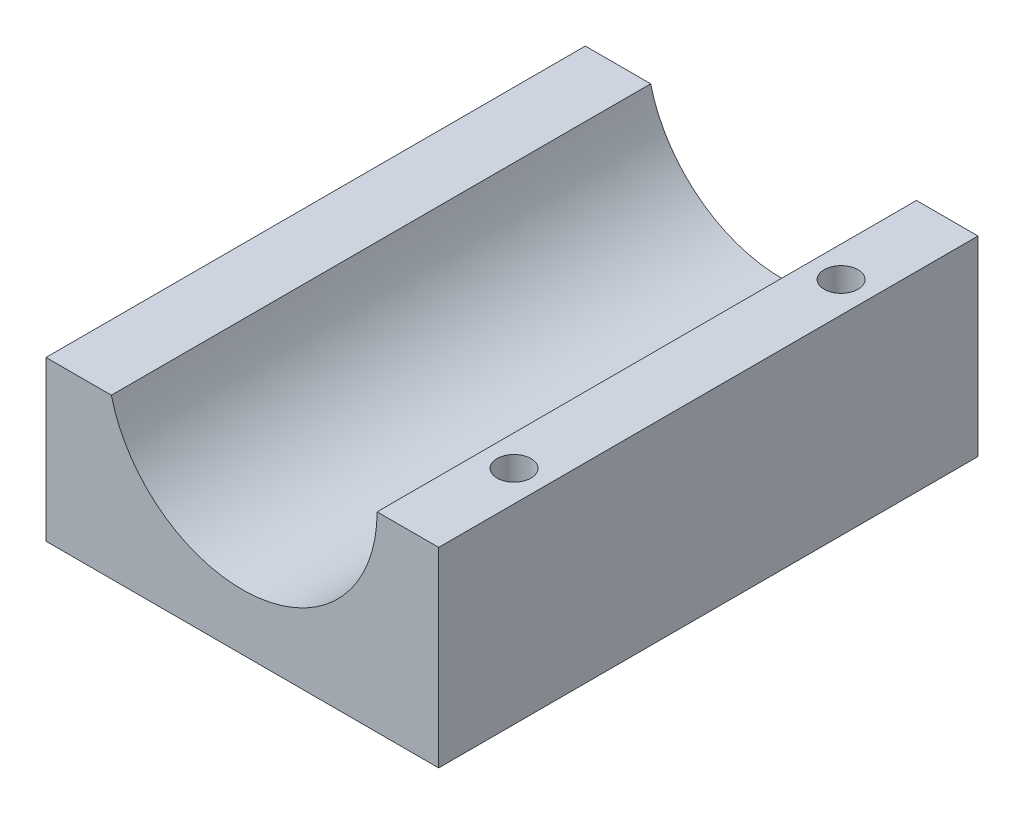
SolidWorks part; units mm, degrees
ref_plane "Front Plane" through (0, 0, 0) normal (0, 0, 1) x (1, 0, 0)
ref_plane "Top Plane" through (0, 0, 0) normal (0, 1, 0) x (1, 0, 0)
ref_plane "Right Plane" through (0, 0, 0) normal (1, 0, 0) x (0, 0, -1)
sketch "Sketch2" plane through (0, 0, 0) normal (0, 1, 0) x (1, 0, 0)
  line L1 (0, 0) -> (18.5, 0)
  line L2 (0, 0) -> (0, 25.41)
  line L3 (0, 25.41) -> (18.5, 25.41)
  line L4 (18.5, 0) -> (18.5, 25.41)
extrude "Boss-Extrude1" add sketch "Sketch2" along normal blind 9
sketch "Sketch6" plane through (0, 0, 0) normal (0, 0, 1) x (1, 0, 0)
  line L0 (0, 9) -> (18.5, 9) construction
  line L1 (2.9, 9) -> (15.6, 9)
  arc A0 (2.9, 9) -> (15.6, 9) centre (9.25, 9) ccw
extrude "Cut-Extrude1" cut sketch "Sketch6" against normal blind 25.41
sketch "Sketch7" plane through (0, 0, 0) normal (0, -1, 0) x (-1, 0, 0)
  line L0 (0, 0) -> (0, 5)
  line L1 (0, 25.41) -> (0, 0) construction
  line L2 (0, 5) -> (-18.5, 5)
  line L3 (-18.5, 0) -> (-18.5, 25.41) construction
  line L4 (0, 25.41) -> (0, 20.41)
  line L5 (0, 20.41) -> (-18.5, 20.41)
sketch "Sketch10" plane through (0, 9, 0) normal (0, 1, 0) x (1, 0, 0)
  line L0 (17.05, 25.41) -> (17.05, 20.41)
  line L1 (18.5, 25.41) -> (15.6, 25.41) construction
  line L2 (17.05, 0) -> (17.05, 5)
  line L3 (15.6, 0) -> (18.5, 0) construction
  circle A0 centre (17.05, 20.41) radius 0.8
  circle A1 centre (17.05, 5) radius 0.8
sketch "Sketch14" plane through (0, 0, -25.41) normal (0, 0, -1) x (-1, 0, 0)
  line L0 (0, 9) -> (0, 7.5)
  line L1 (0, 9) -> (0, 0) construction
  line L2 (0, 7.5) -> (-3.2467, 7.5)
  line L3 (-3.2467, 7.5) -> (-2.9, 9)
extrude "Cut-Extrude3" cut sketch "Sketch14" against normal blind 25.41 and the other way through all flip side to cut
extrude "Cut-Extrude4" cut sketch "Sketch10" against normal through all
